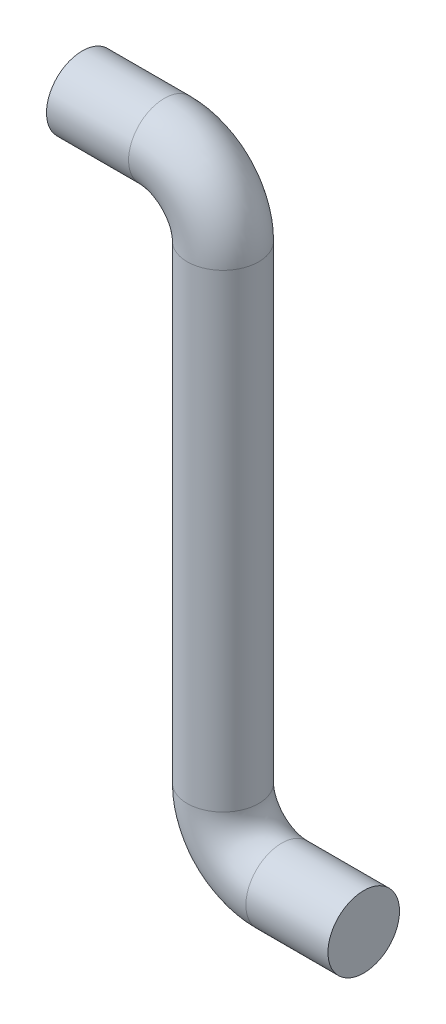
SolidWorks part; units mm, degrees
material "ABS"
ref_plane "Front Plane" through (0, 0, 0) normal (0, 0, 1) x (1, 0, 0)
ref_plane "Top Plane" through (0, 0, 0) normal (0, 1, 0) x (1, 0, 0)
ref_plane "Right Plane" through (0, 0, 0) normal (1, 0, 0) x (0, 0, -1)
sketch "Sketch1" plane through (0, 0, 0) normal (0, 0, 1) x (1, 0, 0)
  line L0 (0, 0) -> (-7, 0)
  line L1 (-12, 5) -> (-12, 45)
  line L2 (-17, 50) -> (-24, 50)
  arc A1 (-12, 5) -> (-7, 0) centre (-7, 5) ccw
  arc A2 (-12, 45) -> (-17, 50) centre (-17, 45) ccw
  point P9 (-12, 0)
  point P12 (-12, 50)
  dimension "D1" = 50
  dimension "D3" = 5
  dimension "D2" = 12
sketch "Sketch2" plane through (0, 0, 0) normal (1, 0, 0) x (0, 0, -1)
  circle A0 centre (0, 0) radius 3.05
  dimension "D1" = 6.1
sweep "Sweep1" add profiles "Sketch2" path "Sketch1"
